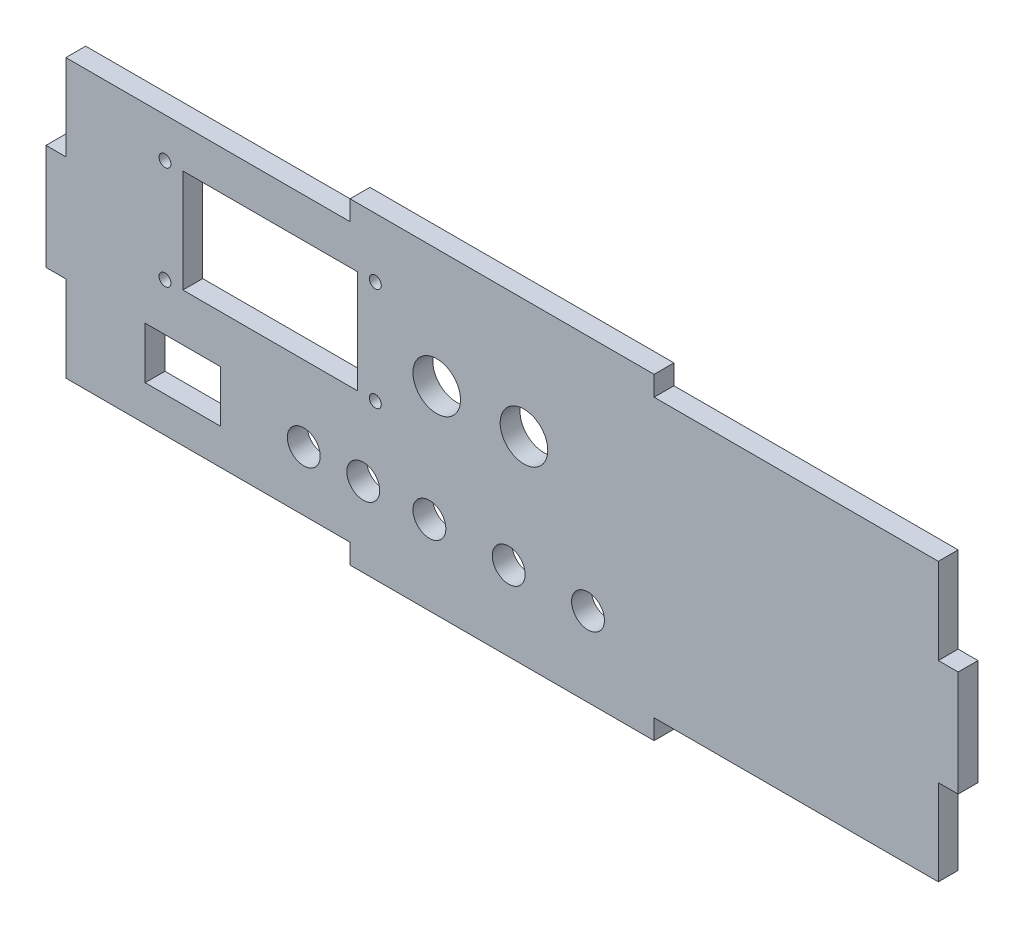
SolidWorks part; units mm, degrees
ref_plane "Alzado" through (0, 0, 0) normal (0, 0, 1) x (1, 0, 0)
ref_plane "Planta" through (0, 0, 0) normal (0, 1, 0) x (1, 0, 0)
ref_plane "Vista lateral" through (0, 0, 0) normal (1, 0, 0) x (0, 0, -1)
sketch "Croquis1" plane through (0, 0, 0) normal (0, 0, 1) x (1, 0, 0)
  line L0 (30, 65) -> (83.04, 65) construction
  line L1 (0, 0) -> (230, 0)
  line L2 (0, 0) -> (0, 80)
  line L3 (0, 80) -> (230, 80)
  line L4 (230, 0) -> (230, 80)
  line L5 (83.04, 65) -> (83.04, 39) construction
  line L6 (83.04, 39) -> (30, 39) construction
  line L7 (30, 39) -> (30, 65) construction
  line L8 (0, 40) -> (-6.7015, 40) construction
  line L9 (0, 53.3333) -> (5, 53.3333)
  line L10 (0, 53.3333) -> (0, 26.6667)
  line L11 (0, 26.6667) -> (5, 26.6667)
  line L12 (5, 53.3333) -> (5, 26.6667)
  line L13 (76.6667, 80) -> (153.3333, 80)
  line L14 (76.6667, 80) -> (76.6667, 75)
  line L15 (76.6667, 75) -> (153.3333, 75)
  line L16 (153.3333, 80) -> (153.3333, 75)
  line L17 (115, 80) -> (115, 87.6964) construction
  line L18 (230, 26.6667) -> (225, 26.6667)
  line L19 (230, 53.3333) -> (225, 53.3333)
  line L20 (225, 53.3333) -> (225, 26.6667)
  line L21 (153.3333, 0) -> (153.3333, 5)
  line L22 (76.6667, 0) -> (76.6667, 5)
  line L23 (76.6667, 5) -> (153.3333, 5)
  line L24 (56.52, 65) -> (56.52, 39) construction
  line L25 (30, 52) -> (83.04, 52) construction
  line L26 (76.6667, 75) -> (0, 75)
  line L27 (34.52, 65) -> (78.52, 65)
  line L28 (34.52, 65) -> (34.52, 39)
  line L29 (34.52, 39) -> (78.52, 39)
  line L30 (78.52, 65) -> (78.52, 39)
  line L31 (34.52, 65) -> (78.52, 39) construction
  line L32 (34.52, 39) -> (78.52, 65) construction
  line L33 (153.3333, 75) -> (230, 75)
  line L34 (5, 0) -> (5, 80)
  line L35 (0, 5) -> (230, 5)
  line L36 (225, 0) -> (225, 80)
  circle A0 centre (30, 65) radius 1.5
  circle A1 centre (83.04, 65) radius 1.5
  circle A2 centre (30, 39) radius 1.5
  circle A3 centre (83.04, 39) radius 1.5
  point P37 (56.52, 52)
  dimension "D3" = 3
  dimension "D1" = 80
  dimension "D2" = 230
  dimension "D4" = 53.04
  dimension "D5" = 26
  dimension "D6" = 30
  dimension "D7" = 15
  dimension "D8" = 26.6667
  dimension "D9" = 26.6667
  dimension "D10" = 76.6667
  dimension "D11" = 76.6667
  dimension "D12" = 5
  dimension "D13" = 5
  dimension "D15" = 26
  dimension "D14" = 44
extrude "Saliente-Extruir1" add sketch "Croquis1" along normal blind 5 contours L35 L36 L20 L33 L15 L26 L34 L12 L23 A3 A2 A1 A0 L27 L30 L29 L28 | L19 L20 L18 L4 | L23 L22 L1 L21 | L12 L9 L2 L11 | L16 L3 L14 L15
sketch "Croquis2" plane through (0, 0, 5) normal (0, 0, 1) x (1, 0, 0)
  line L0 (96.6667, 20) -> (116.6667, 20) construction
  line L3 (116.6667, 20) -> (136.6667, 20) construction
  line L5 (76.6667, 0) -> (76.6667, 5) construction
  line L6 (153.3333, 5) -> (225, 5) construction
  circle A0 centre (96.6667, 20) radius 4.15
  circle A1 centre (116.6667, 20) radius 4.15
  circle A2 centre (136.6667, 20) radius 4.15
  point P4 (126.6667, 20)
  dimension "D1" = 8.3
  dimension "D2" = 15
  dimension "D3" = 20
  dimension "D4" = 20
  dimension "D5" = 20
extrude "Cortar-Extruir1" cut sketch "Croquis2" against normal blind 10
sketch "Croquis3" plane through (0, 0, 5) normal (0, 0, 1) x (1, 0, 0)
  line L0 (34.52, 39) -> (78.52, 39) construction
  line L1 (25, 27) -> (44, 27)
  line L2 (25, 27) -> (25, 14)
  line L3 (25, 14) -> (44, 14)
  line L4 (44, 27) -> (44, 14)
  line L6 (5, 5) -> (5, 26.6667) construction
  dimension "D1" = 19
  dimension "D2" = 13
  dimension "D3" = 12
  dimension "D4" = 20
extrude "Cortar-Extruir2" cut sketch "Croquis3" against normal blind 10
sketch "Croquis4" plane through (0, 0, 5) normal (0, 0, 1) x (1, 0, 0)
  line L0 (65, 20) -> (80, 20) construction
  line L3 (5, 53.3333) -> (5, 75) construction
  line L4 (5, 5) -> (76.6667, 5) construction
  circle A0 centre (65, 20) radius 4.15
  circle A1 centre (80, 20) radius 4.15
  dimension "D1" = 8.3
  dimension "D4" = 15
  dimension "D2" = 15
  dimension "D3" = 60
extrude "Cortar-Extruir3" cut sketch "Croquis4" against normal blind 10
sketch "Croquis5" plane through (0, 0, 5) normal (0, 0, 1) x (1, 0, 0)
  line L0 (98.52, 50) -> (120.52, 50) construction
  line L1 (34.52, 65) -> (78.52, 65) construction
  line L2 (78.52, 65) -> (78.52, 39) construction
  circle A0 centre (98.52, 50) radius 6
  circle A1 centre (120.52, 50) radius 6
  dimension "D1" = 12
  dimension "D2" = 12
  dimension "D3" = 22
  dimension "D4" = 15
  dimension "D5" = 20
extrude "Cortar-Extruir4" cut sketch "Croquis5" against normal blind 10
